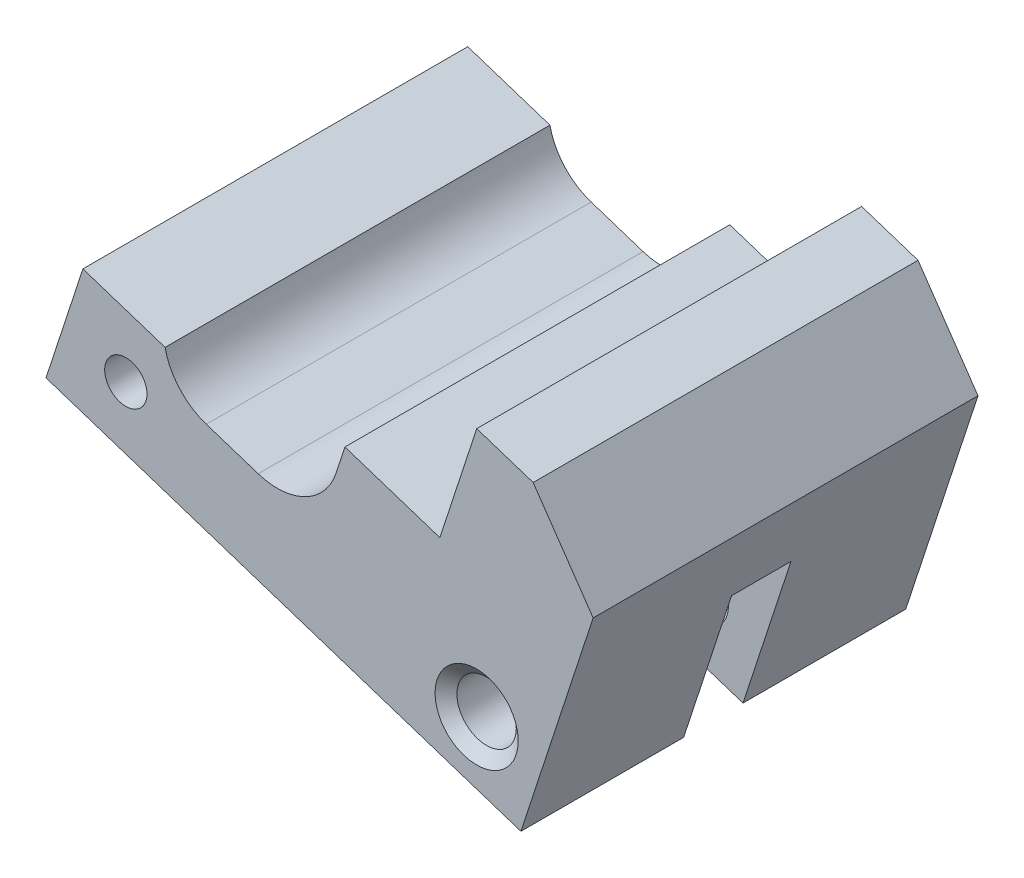
SolidWorks part; units mm, degrees
material "6061-T6 (SS)"
ref_plane "Front Plane" through (0, 0, 0) normal (0, 0, 1) x (1, 0, 0)
ref_plane "Top Plane" through (0, 0, 0) normal (0, 1, 0) x (1, 0, 0)
ref_plane "Right Plane" through (0, 0, 0) normal (1, 0, 0) x (0, 0, -1)
sketch "Sketch1" plane through (0, 0, 0) normal (0, 0, 1) x (1, 0, 0)
  line L0 (7.0876, -81.9967) -> (12.0212, -66.9078) construction
  line L1 (8.0167, -68.9388) -> (7.03, -71.9566)
  line L2 (0.0077, -73.001) -> (-12.0634, -69.0541)
  line L3 (-14.0369, -75.0896) -> (11.3653, -83.3954)
  line L4 (12.0212, -66.9078) -> (15.2291, -71.5783)
  line L6 (8.0167, -68.9388) -> (11.0345, -69.9256) construction
  line L7 (9.0034, -65.9211) -> (8.0167, -68.9388)
  line L8 (12.0212, -66.9078) -> (9.0034, -65.9211)
  line L9 (-12.0634, -69.0541) -> (-14.0369, -75.0896)
  line L10 (11.3653, -83.3954) -> (15.2291, -71.5783)
  line L11 (-42.3168, -73.5908) -> (-38.467, -73.5908) construction
  line L13 (7.03, -71.9566) -> (0.9944, -69.9832)
  line L14 (0.9944, -69.9832) -> (0.0077, -73.001)
  dimension "D2" = 19.05
  dimension "D3" = 15.875
  dimension "D4" = 3.175
  dimension "D5" = 3.175
  dimension "D6" = 6.35
  dimension "D7" = 3.175
  dimension "D8" = 6.35
extrude "Boss-Extrude1" add sketch "Sketch1" along normal offset from surface (20.5861 mm away) 1.27 from offset 1.27
hole_wizard "#4-40 Tapped Hole1" positions "Sketch3" profile "Sketch2" tap size "#4-40" standard "ANSI Inch" end condition through all
sketch "Sketch3" plane through (0, 0, 21.8561) normal (0, 0, 1) x (1, 0, 0)
  line L0 (-14.0369, -75.0896) -> (-12.0634, -69.0541) construction
  line L1 (-13.0501, -72.0719) -> (12.352, -80.3776) construction
  line L2 (15.2291, -71.5783) -> (11.3653, -83.3954) construction
  line L4 (11.3653, -83.3954) -> (-14.0369, -75.0896) construction
  point P0 (-9.7668, -73.1454)
  dimension "D1" = 3.4544
sketch "Sketch2" plane through (-9.7668, -73.1454, 21.8561) normal (1, 0, 0) x (0, -1, 0)
  line L0 (0, 0) -> (0, 20.5861)
  line L1 (0, 20.5861) -> (1.1303, 20.5861)
  line L2 (1.1303, 20.5861) -> (1.1303, 0)
  line L5 (1.1303, 0) -> (0, 0)
  line L11 (0, -6.35) -> (0, 107.95) construction
  dimension "Thru Tap Drill Dia." = 2.2606
  dimension "Thru Tap Drill Depth" = 20.5861
cosmetic thread "Hole Thread1" parameters "D2"=2.8448
hole_wizard "1/8 (0.125) Diameter Hole1" positions "Sketch5" profile "Sketch4" hole size "1/8" standard "ANSI Inch" end condition through all
sketch "Sketch5" plane through (0, 0, 21.8561) normal (0, 0, 1) x (1, 0, 0)
  line L0 (-13.0501, -72.0719) -> (12.352, -80.3776) construction
  line L1 (-14.0369, -75.0896) -> (-12.0634, -69.0541) construction
  line L2 (15.2291, -71.5783) -> (11.3653, -83.3954) construction
  line L6 (11.3653, -83.3954) -> (-14.0369, -75.0896) construction
  line L7 (8.9976, -79.2808) -> (2.5847, -98.894) construction
  line L9 (-2.6048, -102.1841) -> (-15.6885, -142.1994) construction
  point P15 (8.9976, -79.2808)
sketch "Sketch4" plane through (8.9976, -79.2808, 21.8561) normal (1, 0, 0) x (0, -1, 0)
  line L0 (0, 0) -> (0, 20.5861)
  line L1 (0, 20.5861) -> (1.5875, 20.5861)
  line L2 (1.5875, 20.5861) -> (1.5875, 0.5328)
  line L3 (1.5875, 0.5328) -> (2.2225, 0)
  line L5 (2.2225, 0) -> (0, 0)
  line L6 (-1.5875, 0.5328) -> (-2.2225, 0) construction
  line L11 (0, -6.35) -> (0, 107.95) construction
  dimension "Thru Hole Dia." = 3.175
  dimension "Thru Hole Depth" = 20.5861
  dimension "Near C'Sink Dia." = 4.445
  dimension "Near C'Sink Angle" = 100
sketch "Sketch6" plane through (-23.5364, -71.9836, 0) normal (-0.3108, -0.9505, 0) x (0.9505, -0.3108, 0)
  line L0 (36.72, 11.5631) -> (26.56, 11.5631) construction
  line L1 (36.72, 21.8561) -> (36.72, 1.27) construction
  line L2 (36.72, 21.8561) -> (9.9944, 21.8561) construction
  line L3 (36.72, 13.1506) -> (26.56, 13.1506)
  line L4 (36.72, 9.9756) -> (26.56, 9.9756)
  arc A0 (36.72, 13.1506) -> (36.72, 9.9756) centre (36.72, 11.5631) cw
  arc A1 (26.56, 13.1506) -> (26.56, 9.9756) centre (26.56, 11.5631) ccw
  dimension "D1" = 10.16
  dimension "D2" = 1.5875
  dimension "D3" = 1.5875
extrude "Cut-Extrude1" cut sketch "Sketch6" against normal blind 8.255
sketch "Sketch8" plane through (0, 0, 21.8561) normal (0, 0, 1) x (1, 0, 0)
  line L0 (-1.6596, -70.7188) -> (-4.4359, -69.811) construction
  line L1 (-2.6857, -73.8573) -> (-5.4621, -72.9495)
  line L2 (-0.6334, -67.5803) -> (-3.4097, -66.6725)
  line L5 (11.3653, -83.3954) -> (-14.0369, -75.0896) construction
  line L7 (2.765, -71.8983) -> (0.1995, -79.7445) construction
  line L8 (-12.0634, -69.0541) -> (0.0077, -73.001) construction
  line L9 (1.4789, -71.745) -> (1.9526, -70.2965)
  line L10 (0.9944, -69.9832) -> (7.03, -71.9566) construction
  line L11 (1.9526, -70.2965) -> (1.5983, -70.1806)
  arc A0 (-2.6857, -73.8573) -> (-0.6334, -67.5803) centre (-1.6596, -70.7188) ccw
  arc A1 (-3.4097, -66.6725) -> (-5.4621, -72.9495) centre (-4.4359, -69.811) ccw
  point P2 (-3.0477, -70.2649)
  point P9 (1.4789, -71.745)
  point P12 (-7.5744, -68.7848)
  line M10 (7.03, -71.9566) -> (0.9944, -69.9832)
  line M11 (0.9944, -69.9832) -> (0.0077, -73.001)
  line M12 (0.0077, -73.001) -> (-12.0634, -69.0541)
  dimension "D1" = 3.302
  dimension "D2" = 1.27
  dimension "D3" = 1.651
  dimension "D4" = 9.525
extrude "Cut-Extrude2" cut sketch "Sketch8" against normal through all contours A1 L1 A0 M12 M10 M11 | A0 L9 M10
